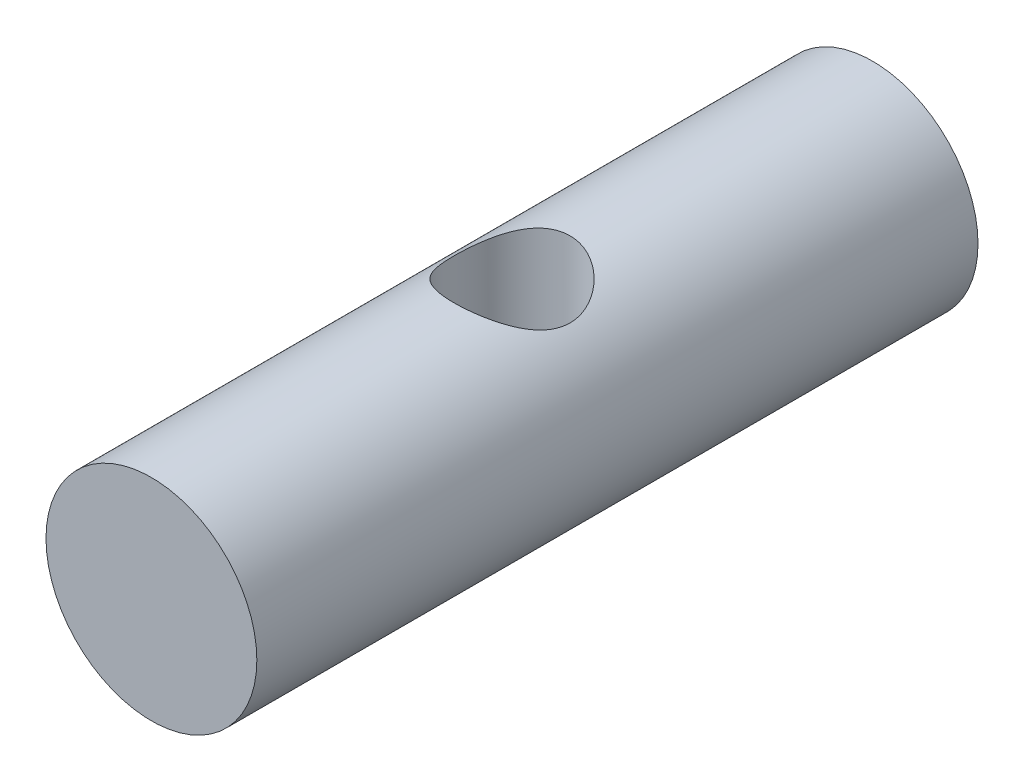
SolidWorks part; units mm, degrees
material "Brass"
ref_plane "Front Plane" through (0, 0, 0) normal (0, 0, 1) x (1, 0, 0)
ref_plane "Top Plane" through (0, 0, 0) normal (0, 1, 0) x (1, 0, 0)
ref_plane "Right Plane" through (0, 0, 0) normal (1, 0, 0) x (0, 0, -1)
sketch "Sketch1" plane through (0, 0, 0) normal (0, 0, 1) x (1, 0, 0)
  circle A0 centre (0, 0) radius 1.7526
  dimension "D1" = 3.5052
extrude "Boss-Extrude1" add sketch "Sketch1" along normal mid plane 11.9888
sketch "Sketch2" plane through (0, 0, 0) normal (0, 1, 0) x (1, 0, 0)
  circle A0 centre (0, 0) radius 0.9652
  dimension "D1" = 1.9304
extrude "Cut-Extrude1" cut sketch "Sketch2" against normal mid plane 6.9088
